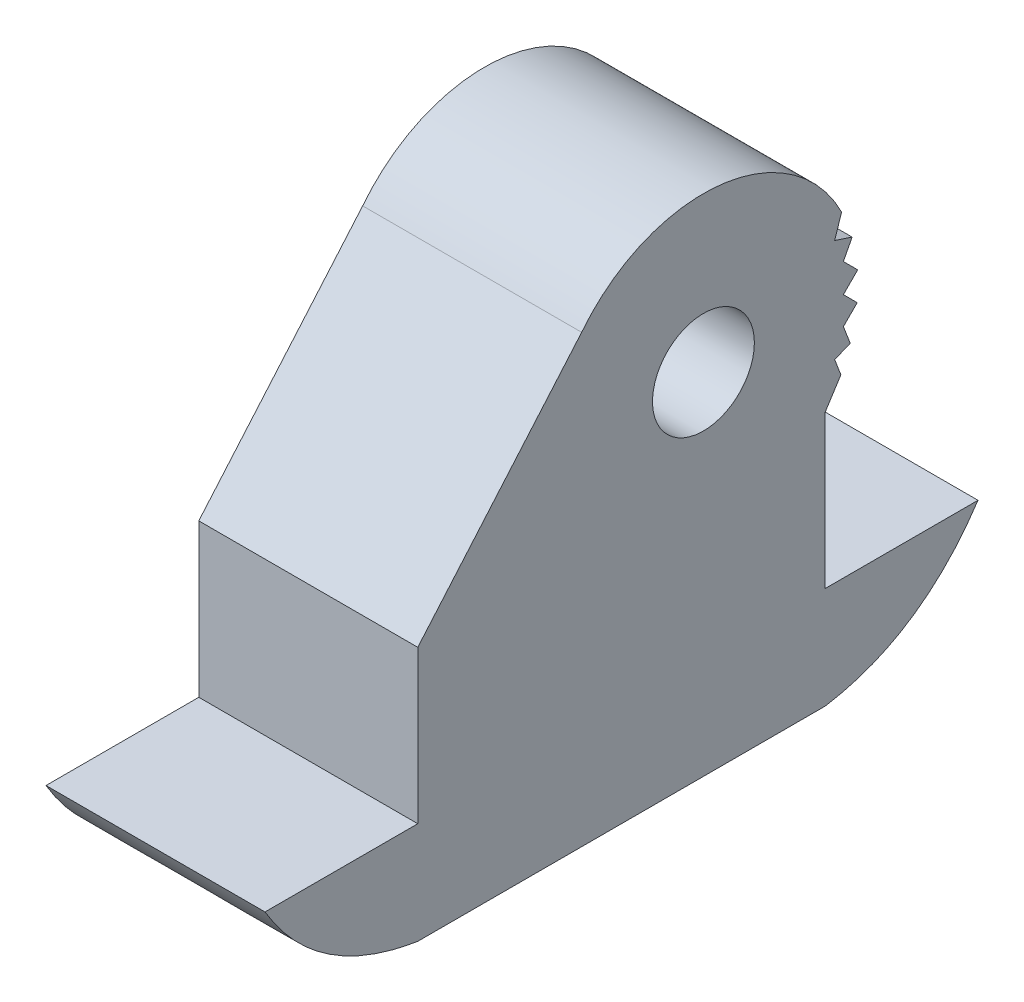
SolidWorks part; units mm, degrees
material "Duranickel(R) 301"
ref_plane "前视基准面" through (0, 0, 0) normal (0, 0, 1) x (1, 0, 0)
ref_plane "上视基准面" through (0, 0, 0) normal (0, 1, 0) x (1, 0, 0)
ref_plane "右视基准面" through (0, 0, 0) normal (1, 0, 0) x (0, 0, -1)
other "Configuration Table"
sketch "草图1" plane through (0, 0, 0) normal (0, 1, 0) x (1, 0, 0)
  line L1 (-2.15, 4) -> (2.15, 4)
  line L2 (-2.15, 4) -> (-2.15, -4)
  line L3 (-2.15, -4) -> (2.15, -4)
  line L4 (2.15, 4) -> (2.15, -4)
  line L5 (-2.15, 4) -> (2.15, -4) construction
  line L6 (-2.15, -4) -> (2.15, 4) construction
  point P0 (0, 0)
  dimension "D1" = 8
  dimension "D2" = 4.3
extrude "凸台-拉伸1" add sketch "草图1" along normal blind 5
sketch "草图2" plane through (2.15, 0, 0) normal (1, 0, 0) x (0, 0, -1)
  line L0 (-4, 2) -> (-7, 2)
  line L1 (-4, 5) -> (-4, 0) construction
  line L2 (4, 2) -> (7, 2)
  line L3 (4, 5) -> (4, 0) construction
  line L4 (-4, 2) -> (-4, 0)
  line L5 (4, 2) -> (4, 0)
  spline S0 degree 2 poles (-7, 2) (-6.0027, 0.3172) (-4, 0) knots 0 0 0 1 1 1
  spline S1 degree 2 poles (4, 0) (5.8688, 0.296) (7, 2) knots 0 0 0 1 1 1
  dimension "D1" = 2
  dimension "D2" = 3
extrude "凸台-拉伸2" add sketch "草图2" against normal up to surface (4.3 mm away) up to face at (-2.15, 2.5, 0)
sketch "草图3" plane through (2.15, 0, 0) normal (1, 0, 0) x (0, 0, -1)
  line L0 (-4, 5) -> (-0.7822, 8.7473)
  line L2 (4, 5) -> (-4, 5)
  line L3 (-0.7822, 8.7473) -> (4, 5) construction
  line L4 (4.322, 8.24) -> (4.1849, 7.8252)
  line L5 (4.1849, 7.8252) -> (4.5288, 7.7115)
  line L6 (4.5288, 7.7115) -> (4.3569, 7.3815)
  line L7 (4.3569, 7.3815) -> (4.6382, 7.0995)
  line L8 (4.6382, 7.0995) -> (4.3569, 6.8187)
  line L9 (4.3569, 6.8187) -> (4.6289, 6.5461)
  line L10 (4.6289, 6.5461) -> (4.3569, 6.2746)
  line L11 (4.3569, 6.2746) -> (4.4929, 5.9195)
  line L12 (4.4929, 5.9195) -> (4.1849, 5.8015)
  line L13 (4.1849, 5.8015) -> (4.3081, 5.48)
  line L14 (4.3081, 5.48) -> (4, 5)
  arc A0 (-0.7822, 8.7473) -> (4, 5) centre (1.6089, 6.8737) cw construction
  circle A1 centre (1.6089, 6.8737) radius 1
  arc A2 (-0.7822, 8.7473) -> (4.322, 8.24) centre (1.6089, 6.8737) cw
extrude "凸台-拉伸3" add sketch "草图3" against normal up to surface (4.3 mm away) up to face at (-2.15, 2.25, -0.375)
